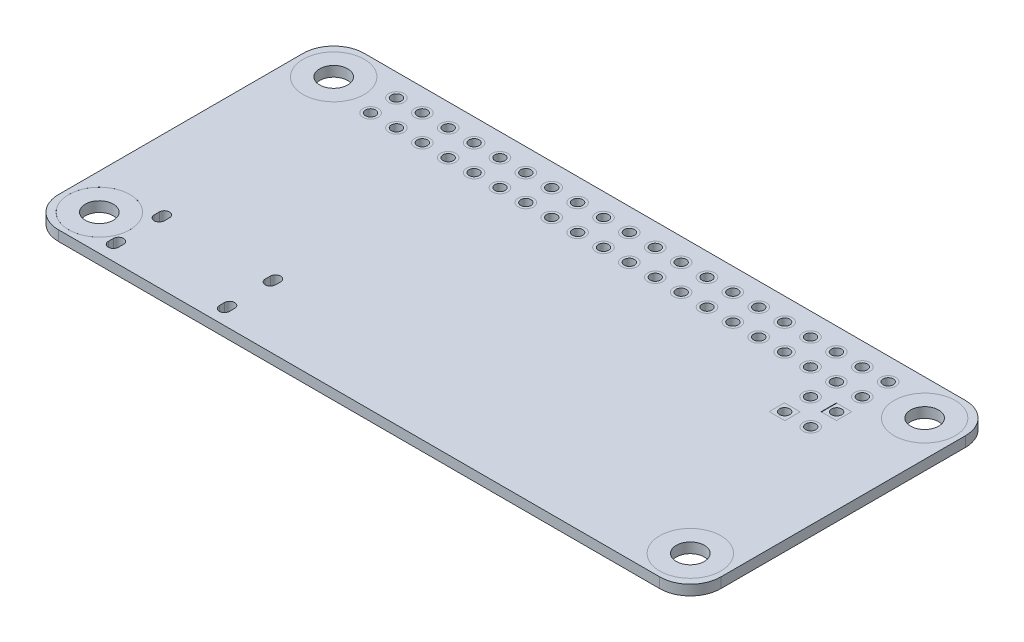
SolidWorks part; units mm, degrees
ref_plane "Front Plane" through (0, 0, 0) normal (0, 0, 1) x (1, 0, 0)
ref_plane "Top Plane" through (0, 0, 0) normal (0, 1, 0) x (1, 0, 0)
ref_plane "Right Plane" through (0, 0, 0) normal (1, 0, 0) x (0, 0, -1)
sketch "Sketch1" plane through (0, 0, 0) normal (0, 1, 0) x (1, 0, 0)
  line L0 (-27.4768, 39.9178) -> (-27.4768, -37.6558) construction
  line L1 (-29.5, -15) -> (29.5, -15)
  line L2 (-32.5, -12) -> (-32.5, 12)
  line L3 (-29.5, 15) -> (29.5, 15)
  line L4 (32.5, -12) -> (32.5, 12)
  line L5 (-32.5, -15) -> (32.5, 15) construction
  line L6 (-32.5, 15) -> (32.5, -15) construction
  line L7 (0, 0) -> (0, 39.9178) construction
  line L9 (-25.5, 14.1112) -> (25.5, 14.1112) construction
  line L10 (-25.5, 14.1112) -> (-25.5, 8.9112) construction
  line L11 (-25.5, 8.9112) -> (25.5, 8.9112) construction
  line L12 (25.5, 14.1112) -> (25.5, 8.9112) construction
  line L13 (23.38, 6.9577) -> (24.88, 6.9577)
  line L14 (23.38, 6.9577) -> (23.38, 8.4577)
  line L15 (23.38, 8.4577) -> (24.88, 8.4577)
  line L16 (24.88, 6.9577) -> (24.88, 8.4577)
  line L17 (23.38, 6.9577) -> (24.88, 8.4577) construction
  line L18 (23.38, 8.4577) -> (24.88, 6.9577) construction
  line L19 (20.8606, 4.4177) -> (22.3606, 4.4177)
  line L20 (20.8606, 4.4177) -> (20.8606, 5.9177)
  line L21 (20.8606, 5.9177) -> (22.3606, 5.9177)
  line L22 (22.3606, 4.4177) -> (22.3606, 5.9177)
  line L23 (20.8606, 4.4177) -> (22.3606, 5.9177) construction
  line L24 (20.8606, 5.9177) -> (22.3606, 4.4177) construction
  arc A0 (-32.5, 12) -> (-29.5, 15) centre (-29.5, 12) cw
  arc A1 (-29.5, -15) -> (-32.5, -12) centre (-29.5, -12) cw
  arc A2 (29.5, -15) -> (32.5, -12) centre (29.5, -12) ccw
  arc A3 (29.5, 15) -> (32.5, 12) centre (29.5, 12) cw
  circle A4 centre (-29, 11.5) radius 3
  circle A5 centre (-29, -11.5) radius 3
  circle A6 centre (29, -11.5) radius 3
  circle A7 centre (-24.13, 12.7877) radius 0.75
  circle A8 centre (-21.59, 12.7877) radius 0.75
  circle A9 centre (-19.05, 12.7877) radius 0.75
  circle A10 centre (-16.51, 12.7877) radius 0.75
  circle A11 centre (-13.97, 12.7877) radius 0.75
  circle A12 centre (-11.43, 12.7877) radius 0.75
  circle A13 centre (-8.89, 12.7877) radius 0.75
  circle A14 centre (-6.35, 12.7877) radius 0.75
  circle A15 centre (-3.81, 12.7877) radius 0.75
  circle A16 centre (-1.27, 12.7877) radius 0.75
  circle A17 centre (1.27, 12.7877) radius 0.75
  circle A18 centre (3.81, 12.7877) radius 0.75
  circle A19 centre (6.35, 12.7877) radius 0.75
  circle A20 centre (8.89, 12.7877) radius 0.75
  circle A21 centre (11.43, 12.7877) radius 0.75
  circle A22 centre (13.97, 12.7877) radius 0.75
  circle A23 centre (16.51, 12.7877) radius 0.75
  circle A24 centre (19.05, 12.7877) radius 0.75
  circle A25 centre (21.59, 12.7877) radius 0.75
  circle A26 centre (24.13, 12.7877) radius 0.75
  circle A27 centre (-21.59, 10.2477) radius 0.75
  circle A28 centre (-19.05, 10.2477) radius 0.75
  circle A29 centre (-16.51, 10.2477) radius 0.75
  circle A30 centre (-13.97, 10.2477) radius 0.75
  circle A31 centre (-11.43, 10.2477) radius 0.75
  circle A32 centre (-8.89, 10.2477) radius 0.75
  circle A33 centre (-6.35, 10.2477) radius 0.75
  circle A34 centre (-3.81, 10.2477) radius 0.75
  circle A35 centre (-1.27, 10.2477) radius 0.75
  circle A36 centre (1.27, 10.2477) radius 0.75
  circle A37 centre (3.81, 10.2477) radius 0.75
  circle A38 centre (6.35, 10.2477) radius 0.75
  circle A39 centre (8.89, 10.2477) radius 0.75
  circle A40 centre (11.43, 10.2477) radius 0.75
  circle A41 centre (13.97, 10.2477) radius 0.75
  circle A42 centre (16.51, 10.2477) radius 0.75
  circle A43 centre (19.05, 10.2477) radius 0.75
  circle A44 centre (21.59, 10.2477) radius 0.75
  circle A45 centre (24.13, 10.2477) radius 0.75
  circle A46 centre (-24.13, 10.2477) radius 0.75
  circle A47 centre (21.59, 7.7077) radius 0.75
  circle A48 centre (24.1506, 5.1677) radius 0.75
  circle A49 centre (29, 11.5) radius 3
  point P0 (0, 0)
  point P32 (0, 8.9112)
  point P117 (24.13, 7.7077)
  point P122 (21.6106, 5.1677)
  dimension "D3" = 3
  dimension "D4" = 51
  dimension "D5" = 6
  dimension "D11" = 1.5
  dimension "D12" = 2
  dimension "D15" = 1.5
  dimension "D16" = 1.5
  dimension "D27" = 6
  dimension "D28" = 6
  dimension "D1" = 65
  dimension "D2" = 30
  dimension "D6" = 23
  dimension "D7" = 29
  dimension "D8" = 3.5
  dimension "D9" = 5.2
  dimension "D10" = 29
  dimension "D13" = 1.27
  dimension "D14" = 20
  dimension "D17" = 2.54
  dimension "D18" = 2.54
  dimension "D19" = 2.54
  dimension "D20" = 2.54
  dimension "D21" = 2.54
  dimension "D22" = 2.54
  dimension "D23" = 1.5
  dimension "D24" = 1.5
  dimension "D25" = 1.5
  dimension "D26" = 1.5
extrude "Boss-Extrude1" add sketch "Sketch1" along normal blind 1
sketch "Sketch2" plane through (0, 0, 0) normal (0, 1, 0) x (1, 0, 0)
  circle A0 centre (-24.13, 12.7877) radius 0.75 construction
  circle A1 centre (-24.13, 12.7877) radius 0.75
  circle A3 centre (-24.13, 12.7877) radius 0.5
  dimension "D1" = 1
extrude "Boss-Extrude2" add sketch "Sketch2" along normal blind 1 separate body
pattern_linear "LPattern2" count 20 spacing 2.54 along (1, 0, 0) count 2 spacing 2.54 along (0, 0, 1) of bodies 102
sketch "Sketch3" plane through (0, 0, 0) normal (0, 1, 0) x (1, 0, 0)
  line L1 (20.8194, 4.4177) -> (22.3606, 4.4177)
  line L2 (20.8194, 4.4177) -> (20.8194, 5.9177)
  line L3 (20.8194, 5.9177) -> (22.3606, 5.9177)
  line L4 (22.3606, 4.4177) -> (22.3606, 5.9177)
  line L5 (20.8194, 4.4177) -> (22.3606, 5.9177) construction
  line L6 (20.8194, 5.9177) -> (22.3606, 4.4177) construction
  line L7 (23.4212, 6.9577) -> (24.88, 6.9577)
  line L8 (23.4212, 6.9577) -> (23.4212, 8.4577)
  line L9 (23.4212, 8.4577) -> (24.88, 8.4577)
  line L10 (24.88, 6.9577) -> (24.88, 8.4577)
  line L11 (23.4212, 6.9577) -> (24.88, 8.4577) construction
  line L12 (23.4212, 8.4577) -> (24.88, 6.9577) construction
  circle A0 centre (21.59, 7.7077) radius 0.75
  circle A1 centre (21.59, 7.7077) radius 0.5
  circle A2 centre (24.1506, 5.1677) radius 0.75
  circle A3 centre (24.1506, 5.1677) radius 0.5
  circle A4 centre (24.1506, 7.7077) radius 0.5
  circle A5 centre (21.59, 5.1677) radius 0.5
  dimension "D1" = 1
  dimension "D2" = 1
  dimension "D3" = 1
  dimension "D4" = 1
extrude "Boss-Extrude3" add sketch "Sketch3" along normal blind 1 separate body
sketch "Sketch4" plane through (0, 0, 0) normal (0, 1, 0) x (1, 0, 0)
  circle A0 centre (-29, 11.5) radius 3
  circle A1 centre (-29, 11.5) radius 1.375
  dimension "D1" = 2.75
extrude "Boss-Extrude4" add sketch "Sketch4" along normal blind 1 separate body
mirror "Mirror1" about plane through (0, 0, 0) normal (1, 0, 0) of bodies 147
mirror "Mirror2" about plane through (0, 0, 0) normal (0, 0, 1) of bodies 147 148
sketch "Sketch5" plane through (0, 0, 0) normal (0, -1, 0) x (1, 0, 0)
  line L0 (-25.5788, 13.0395) -> (-25.5788, 13.5395) construction
  line L1 (-26.0788, 13.0395) -> (-26.0788, 13.5395)
  line L2 (-25.0788, 13.0395) -> (-25.0788, 13.5395)
  line L3 (-14.6788, 13.0395) -> (-14.6788, 13.5395) construction
  line L4 (-15.1788, 13.0395) -> (-15.1788, 13.5395)
  line L5 (-14.1788, 13.0395) -> (-14.1788, 13.5395)
  line L6 (-14.6788, 8.5395) -> (-14.6788, 9.0395) construction
  line L7 (-15.1788, 8.5395) -> (-15.1788, 9.0395)
  line L8 (-14.1788, 8.5395) -> (-14.1788, 9.0395)
  line L9 (-25.5788, 8.5395) -> (-25.5788, 9.0395) construction
  line L10 (-26.0788, 8.5395) -> (-26.0788, 9.0395)
  line L11 (-25.0788, 8.5395) -> (-25.0788, 9.0395)
  arc A0 (-26.0788, 13.0395) -> (-25.0788, 13.0395) centre (-25.5788, 13.0395) ccw
  arc A1 (-25.0788, 13.5395) -> (-26.0788, 13.5395) centre (-25.5788, 13.5395) ccw
  arc A2 (-15.1788, 13.0395) -> (-14.1788, 13.0395) centre (-14.6788, 13.0395) ccw
  arc A3 (-14.1788, 13.5395) -> (-15.1788, 13.5395) centre (-14.6788, 13.5395) ccw
  arc A4 (-15.1788, 8.5395) -> (-14.1788, 8.5395) centre (-14.6788, 8.5395) ccw
  arc A5 (-14.1788, 9.0395) -> (-15.1788, 9.0395) centre (-14.6788, 9.0395) ccw
  arc A6 (-26.0788, 8.5395) -> (-25.0788, 8.5395) centre (-25.5788, 8.5395) ccw
  arc A7 (-25.0788, 9.0395) -> (-26.0788, 9.0395) centre (-25.5788, 9.0395) ccw
  point P2 (-25.5788, 13.2895)
  point P11 (-14.6788, 13.2895)
  point P18 (-14.6788, 8.7895)
  point P25 (-25.5788, 8.7895)
  dimension "D2" = 0.5
  dimension "D1" = 0.5
  dimension "D3" = 2
extrude "Cut-Extrude1" cut sketch "Sketch5" against normal blind 1
